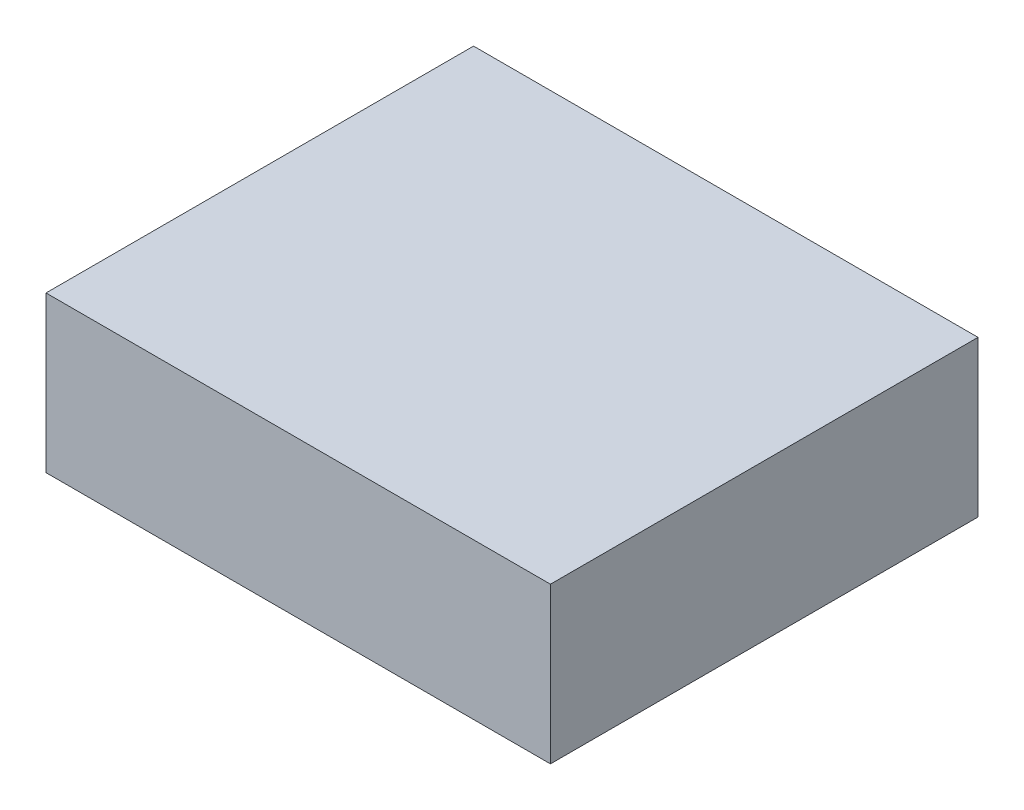
SolidWorks part; units mm, degrees
ref_plane "Front Plane" through (0, 0, 0) normal (0, 0, 1) x (1, 0, 0)
ref_plane "Top Plane" through (0, 0, 0) normal (0, 1, 0) x (1, 0, 0)
ref_plane "Right Plane" through (0, 0, 0) normal (1, 0, 0) x (0, 0, -1)
sketch "Sketch1" plane through (0, 0, 0) normal (0, 1, 0) x (1, 0, 0)
  line L1 (-34.163, -28.956) -> (34.163, -28.956)
  line L2 (-34.163, -28.956) -> (-34.163, 28.956)
  line L3 (-34.163, 28.956) -> (34.163, 28.956)
  line L4 (34.163, -28.956) -> (34.163, 28.956)
  line L5 (-34.163, -28.956) -> (34.163, 28.956) construction
  line L6 (-34.163, 28.956) -> (34.163, -28.956) construction
  point P0 (0, 0)
  dimension "D1" = 68.326
  dimension "D2" = 57.912
extrude "Boss-Extrude1" add sketch "Sketch1" along normal blind 21.082
